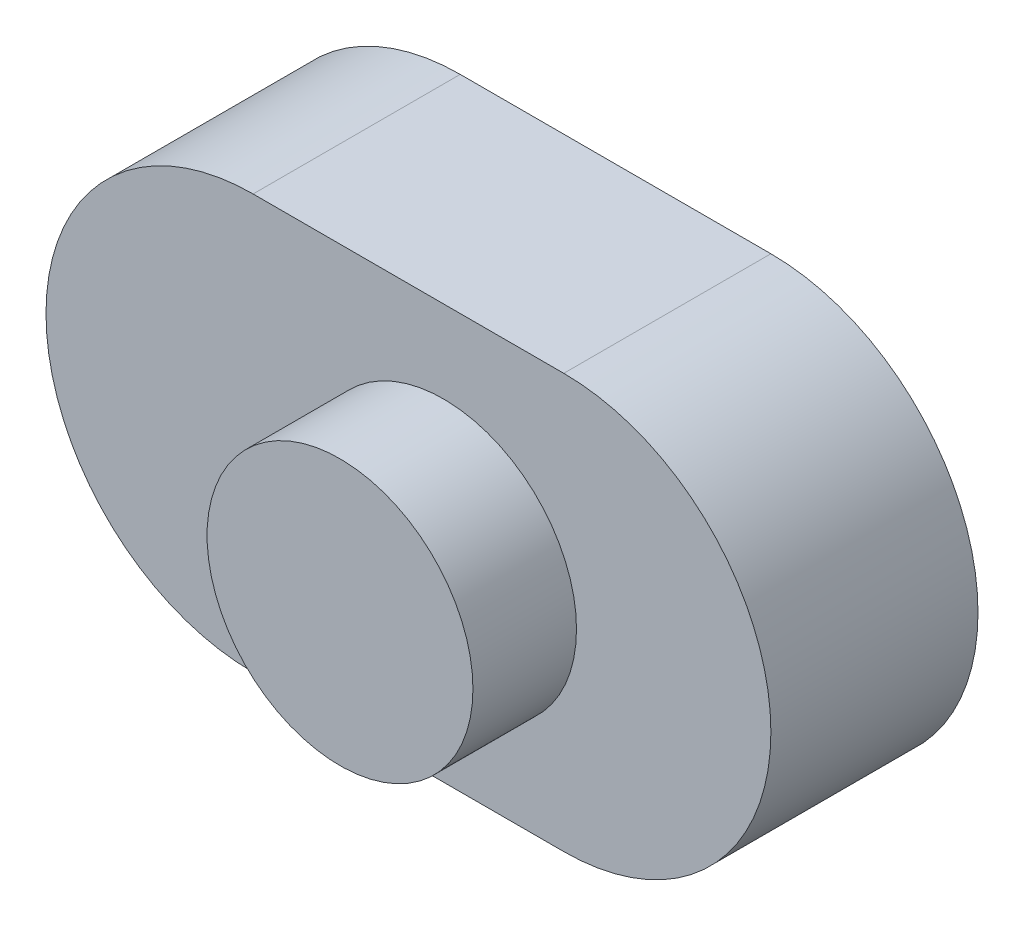
SolidWorks part; units mm, degrees
ref_plane "Alzado" through (0, 0, 0) normal (0, 0, 1) x (1, 0, 0)
ref_plane "Planta" through (0, 0, 0) normal (0, 1, 0) x (1, 0, 0)
ref_plane "Vista lateral" through (0, 0, 0) normal (1, 0, 0) x (0, 0, -1)
sketch "Croquis1" plane through (0, 0, 0) normal (0, 0, 1) x (1, 0, 0)
  line L0 (-55.3698, -2.5069) -> (-40.3698, -2.5069) construction
  line L1 (-55.3698, 7.4931) -> (-40.3698, 7.4931)
  line L2 (-55.3698, -12.5069) -> (-40.3698, -12.5069)
  arc A0 (-55.3698, 7.4931) -> (-55.3698, -12.5069) centre (-55.3698, -2.5069) ccw
  arc A1 (-40.3698, -12.5069) -> (-40.3698, 7.4931) centre (-40.3698, -2.5069) ccw
  point P2 (-47.8698, -2.5069)
  dimension "D1" = 15
  dimension "D2" = 20
extrude "Saliente-Extruir1" add sketch "Croquis1" along normal blind 10
sketch "Croquis2" plane through (0, 0, 10) normal (0, 0, 1) x (1, 0, 0)
  circle A0 centre (-46.1745, -2.8979) radius 6.4186
extrude "Saliente-Extruir2" add sketch "Croquis2" along normal blind 5
